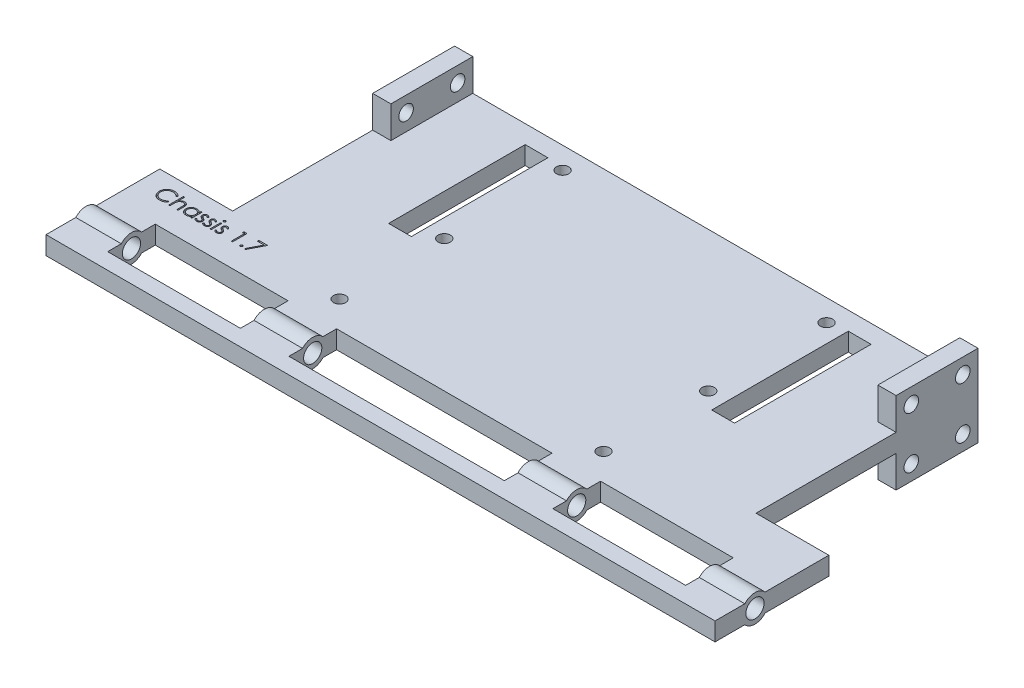
SolidWorks part; units mm, degrees
ref_plane "Front Plane" through (0, 0, 0) normal (0, 0, 1) x (1, 0, 0)
ref_plane "Top Plane" through (0, 0, 0) normal (0, 1, 0) x (1, 0, 0)
ref_plane "Right Plane" through (0, 0, 0) normal (1, 0, 0) x (0, 0, -1)
sketch "Sketch1" plane through (0, 0, 0) normal (0, 1, 0) x (1, 0, 0)
  line L0 (57.5, 0) -> (57.5, -73.7765) construction
  line L1 (0, 0) -> (115, 0)
  line L5 (28.5, -20.443) -> (24.5, -20.443) construction
  line L6 (57.5, -53.7765) -> (57.5, -73.7765) construction
  line L7 (28.5, -53.7765) -> (86.5, -53.7765) construction
  line L8 (28.5, -53.7765) -> (28.5, -30.7765) construction
  line L9 (28.5, -30.7765) -> (86.5, -30.7765) construction
  line L10 (86.5, -53.7765) -> (86.5, -30.7765) construction
  line L11 (28.5, -53.7765) -> (28.5, -4.7765) construction
  line L12 (28.5, -4.7765) -> (86.5, -4.7765) construction
  line L13 (86.5, -4.7765) -> (86.5, -53.7765) construction
  line L17 (0, -48.7765) -> (-16, -48.7765)
  line L18 (-16, -73.7765) -> (-16, -48.7765)
  line L19 (-16, -73.7765) -> (-16, 0) construction
  line L20 (-16, 0) -> (0, 0) construction
  line L21 (0, -48.7765) -> (0, 0)
  line L24 (131, -73.7765) -> (131, -48.7765)
  line L25 (131, -48.7765) -> (115, -48.7765)
  line L26 (115, -48.7765) -> (115, 0)
  line L27 (131, -73.7765) -> (-16, -73.7765)
  line L28 (20.9372, 0) -> (20.9372, -4) construction
  line L29 (19.5, -4) -> (24.5, -4)
  line L30 (19.5, -4) -> (19.5, -34)
  line L31 (19.5, -34) -> (24.5, -34)
  line L32 (24.5, -4) -> (24.5, -34)
  line L33 (86.5, -45.1604) -> (90.5, -45.1604) construction
  line L34 (95.5, -34) -> (90.5, -34)
  line L35 (90.5, -4) -> (90.5, -34)
  line L36 (95.5, -4) -> (90.5, -4)
  line L37 (95.5, -4) -> (95.5, -34)
  line L38 (92.015, -68.7765) -> (92.015, -73.7765) construction
  circle A0 centre (28.5, -30.7765) radius 1.35
  circle A1 centre (28.5, -53.7765) radius 1.35
  circle A2 centre (86.5, -30.7765) radius 1.35
  circle A3 centre (86.5, -53.7765) radius 1.35
  circle A4 centre (86.5, -4.7765) radius 1.35
  circle A5 centre (28.5, -4.7765) radius 1.35
  point P9 (57.5, 0)
  point P14 (57.5, -30.7765)
  point P16 (57.5, -53.7765)
  dimension "D5" = 2.7
  dimension "D6" = 2.7
  dimension "D9" = 2.7
  dimension "D10" = 2.7
  dimension "D11" = 2.7
  dimension "D12" = 2.7
  dimension "D1" = 115
  dimension "D2" = 48.7765
  dimension "D3" = 23
  dimension "D4" = 58
  dimension "D7" = 20
  dimension "D8" = 49
  dimension "D13" = 16
  dimension "D14" = 25
  dimension "D15" = 16
  dimension "D16" = 25
  dimension "D17" = 4
  dimension "D18" = 5
  dimension "D19" = 30
  dimension "D20" = 4
extrude "Base Chassis" add sketch "Sketch1" along normal mid plane 4
sketch "Sketch14" plane through (0, 2, 0) normal (0, 1, 0) x (1, 0, 0)
  text T0 "Chassis 1.7"
extrude "Text" cut sketch "Sketch14" against normal blind 0.5
sketch "Sketch7" plane through (0, 0, 0) normal (-1, 0, 0) x (0, 0, 1)
  line L12 (0, -9) -> (0, 9)
  line L13 (0, 9) -> (18, 9)
  line L15 (0, -2) -> (73.7765, -2) construction
  line L23 (0, -9) -> (18, 9) construction
  line L24 (9, 0) -> (3.3431, 5.6569) construction
  line L28 (0, -9) -> (18, -9)
  line L35 (18, -9) -> (18, 9)
  line L36 (0, 0) -> (9, 0) construction
  line L37 (9, 0) -> (9, -9) construction
  circle A4 centre (9, 0) radius 8 construction
  circle A5 centre (3.3431, 5.6569) radius 1.6
  circle A9 centre (14.6569, 5.6569) radius 1.6
  circle A10 centre (14.6569, -5.6569) radius 1.6
  circle A11 centre (3.3431, -5.6569) radius 1.6
  point P1 (0, 0)
  point P2 (0, 0)
  point P24 (9, 0)
  dimension "D3" = 16
  dimension "D4" = 3.2
  dimension "D5" = 9
  dimension "D1" = 18
  dimension "D6" = 9
extrude "Mount Holes" add sketch "Sketch7" against normal blind 4
sketch "Sketch8" plane through (-16, 0, 0) normal (-1, 0, 0) x (0, 0, 1)
  line L0 (9, 9) -> (9, -9) construction
  line L1 (18, 9) -> (0, 9) construction
  line L3 (65, 3) -> (65, -3) construction
  line L6 (9, 0) -> (65, 0) construction
  line L7 (0, -9) -> (18, -9) construction
  circle A0 centre (65, 0) radius 3
  dimension "D2" = 6
  dimension "D1" = 56
extrude "Shaft Extrude" add sketch "Sketch8" against normal through all
sketch "Sketch20" plane through (-16, 0, 0) normal (-1, 0, 0) x (0, 0, 1)
  circle A0 centre (65, 0) radius 2
  dimension "D1" = 4
extrude "Shaft Cut" cut sketch "Sketch20" against normal through all
sketch "Sketch10" plane through (0, 2, 0) normal (0, 1, 0) x (1, 0, 0)
  line L0 (57.5, 0) -> (57.5, -73.7765) construction
  line L1 (115, 0) -> (4, 0) construction
  line L2 (0, -73.7765) -> (115, -73.7765) construction
  line L3 (-16, -65) -> (57.5, -65) construction
  line L5 (-6, -65) -> (-6, -62.7639)
  line L11 (115, -73.7765) -> (115, -66.2361) construction
  line L19 (-6, -62.7639) -> (-6, -59.7639)
  line L20 (-6, -59.7639) -> (23.1719, -59.7639)
  line L21 (23.1719, -59.7639) -> (23.1719, -62.7639)
  line L22 (23.1719, -62.7639) -> (23.1719, -65)
  line L23 (23.1719, -65) -> (23.1719, -67.2361)
  line L24 (23.1719, -70.2361) -> (33.8281, -70.2361) construction
  line L25 (23.1719, -67.2361) -> (23.1719, -70.2361)
  line L26 (23.1719, -70.2361) -> (-6, -70.2361)
  line L27 (-6, -70.2361) -> (-6, -67.2361)
  line L28 (-6, -67.2361) -> (-6, -65)
  line L29 (-16, -73.7765) -> (-6, -73.7765) construction
  line L30 (-6, -73.7765) -> (-6, -70.2361) construction
  line L31 (23.1719, -59.7639) -> (33.8281, -59.7639) construction
  line L32 (33.8281, -59.7639) -> (33.8281, -62.7639)
  line L33 (33.8281, -62.7639) -> (33.8281, -65)
  line L34 (33.8281, -65) -> (33.8281, -67.2361)
  line L35 (33.8281, -67.2361) -> (33.8281, -70.2361)
  line L36 (33.8281, -70.2361) -> (57.5, -70.2361)
  line L37 (57.5, -70.2361) -> (57.5, -67.2361)
  line L38 (57.5, -67.2361) -> (57.5, -65)
  line L39 (57.5, -65) -> (57.5, -62.7639)
  line L40 (57.5, -62.7639) -> (57.5, -59.7639)
  line L41 (57.5, -59.7639) -> (33.8281, -59.7639)
  line L42 (-16, -73.7765) -> (131, -73.7765) construction
  line L44 (131, -67.2361) -> (-16, -67.2361) construction
  line L46 (-16, -62.7639) -> (-16, -67.2361) construction
  line L47 (-16, -62.7639) -> (131, -62.7639) construction
  dimension "D1" = 3
  dimension "D2" = 3
  dimension "D3" = 10.6562
  dimension "D4" = 10
  dimension "D6" = 23.6719
extrude "Screw Hole" cut sketch "Sketch10" against normal through all both and the other way through all contours L40 L41 L32 L33 L34 L35 L36 L37 L38 L39 | L25 L26 L27 L28 L5 L19 L20 L21 L22 L23
ref_plane "Plane1" through (57.5, 0, 0) normal (-1, 0, 0) x (0, 0, 1)
mirror "Mirror1" about plane through (57.5, 0, 0) normal (-1, 0, 0) of "Screw Hole", "Mount Holes"
ref_plane "Plane2" through (1.1976, 2, 52.3291) normal (0, 0, 1) x (1, 0, 0)
